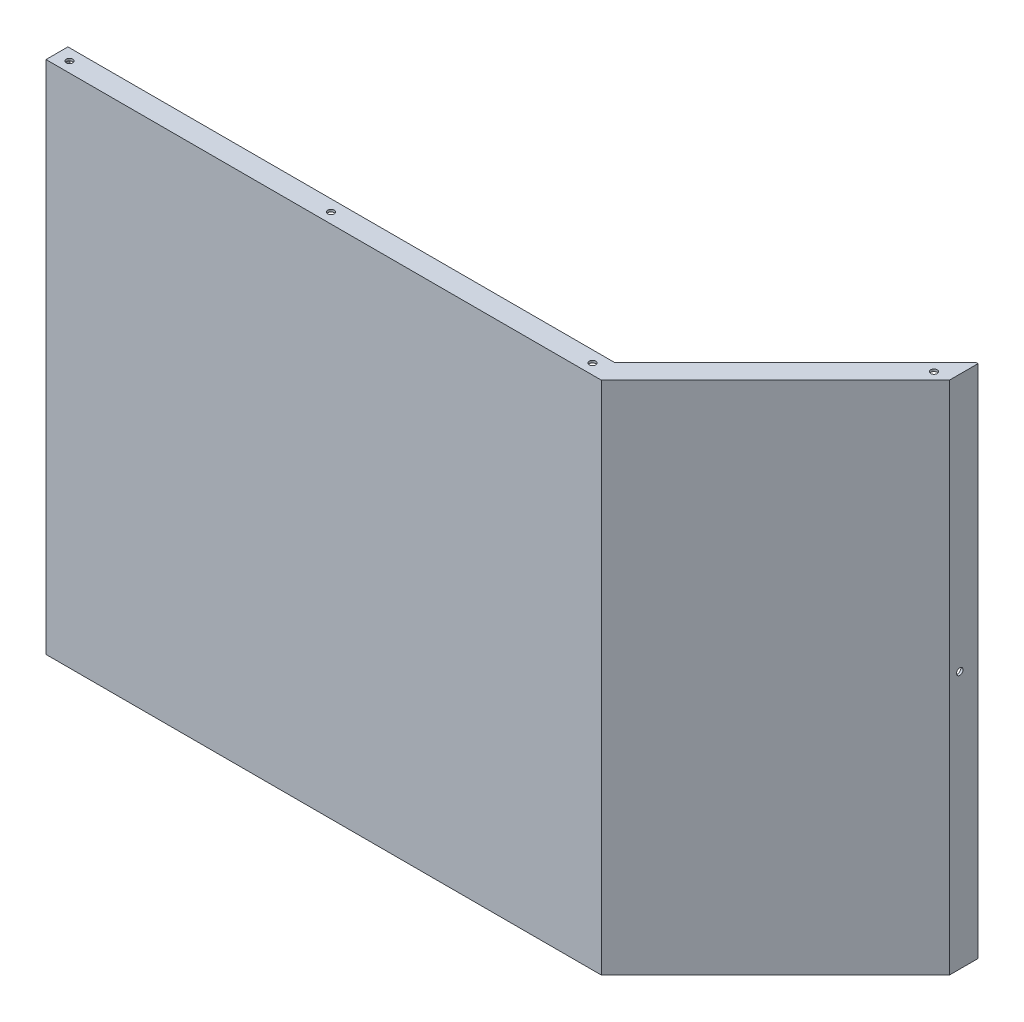
SolidWorks part; units mm, degrees
material "PPS"
ref_plane "Płaszczyzna XY" through (0, 0, 0) normal (0, 0, 1) x (1, 0, 0)
ref_plane "Płaszczyzna XZ" through (0, 0, 0) normal (0, 1, 0) x (1, 0, 0)
ref_plane "Płaszczyzna YZ" through (0, 0, 0) normal (1, 0, 0) x (0, 0, -1)
sketch "Szkic1" plane through (0, 0, 0) normal (0, 1, 0) x (1, 0, 0)
  line L0 (-422.25, 0) -> (0, 0)
  line L1 (0, 0) -> (132, 132)
  line L3 (-424, 0) -> (-424, -1.75)
  line L4 (-424, -1.75) -> (0.7249, -1.75)
  line L5 (133.75, 131.2751) -> (0.7249, -1.75)
  line L6 (-424, 0) -> (-424, 15)
  line L7 (-424, 15) -> (-422.25, 15)
  line L8 (-422.25, 15) -> (-422.25, 0)
  line L9 (132, 132) -> (132, 153.2)
  line L10 (132, 153.2) -> (133.75, 153.2)
  line L11 (133.75, 153.2) -> (133.75, 131.2751)
  dimension "D2" = 424
  dimension "D3" = 1.75
  dimension "D4" = 1.75
  dimension "D5" = 0
  dimension "D6" = 135
  dimension "D7" = 0
  dimension "D8" = 15
  dimension "D9" = 1.75
  dimension "D10" = 15
  dimension "D11" = 1.75
  dimension "D12" = 21.2
  dimension "D13" = 132
extrude "Dodanie-wyciągnięcie1" add sketch "Szkic1" along normal mid plane 394
sketch "Szkic2" plane through (0, -197, 0) normal (0, -1, 0) x (1, 0, 0)
  line L0 (-422.25, -15) -> (-422.25, 0)
  line L1 (-422.25, -15) -> (-424, -15) construction
  line L2 (0, 0) -> (-422.25, 0) construction
  line L3 (-422.25, 0) -> (-422.25, -15) construction
  line L4 (-422.25, 0) -> (0, 0)
  line L5 (0, 0) -> (132, -132)
  line L6 (132, -153.2) -> (132, -132) construction
  line L7 (132, -132) -> (0, 0) construction
  line L8 (132, -132) -> (132, -153.2132)
  line L11 (-422.25, -15) -> (-6.2132, -15)
  line L12 (-6.2132, -15) -> (132, -153.2132)
  dimension "D1" = 15
  dimension "D2" = 135
extrude "Dodanie-wyciągnięcie2" add sketch "Szkic2" against normal blind 1.75
mirror "Lustro1" about plane through (0, 0, 0) normal (0, 1, 0) of "Dodanie-wyciągnięcie2"
sketch "Szkic3" plane through (0, -197, 0) normal (0, -1, 0) x (1, 0, 0)
  line L0 (-424, 1.75) -> (0.7249, 1.75) construction
  line L2 (-424, -15) -> (-424, 1.75) construction
  line L3 (0.7249, 1.75) -> (133.75, -131.2751) construction
  circle A0 centre (-414, -6.25) radius 2.5
  circle A1 centre (-214, -6.25) radius 2.5
  circle A2 centre (-14, -6.25) radius 2.5
  circle A3 centre (122.2215, -131.0603) radius 2.5
  dimension "D1" = 5
  dimension "D2" = 8
  dimension "D3" = 10
  dimension "D4" = 5
  dimension "D5" = 8
  dimension "D6" = 200
  dimension "D7" = 200
  dimension "D8" = 8
  dimension "D9" = 5
  dimension "D10" = 5
  dimension "D11" = 8
  dimension "D12" = 180
extrude "Wytnij-wyciągnięcie1" cut sketch "Szkic3" against normal blind 466
sketch "Szkic4" plane through (133.75, 0, 0) normal (1, 0, 0) x (0, 0, -1)
  line L0 (131.2751, 197) -> (131.2751, -197) construction
  line L1 (131.2751, 197) -> (153.2, 197) construction
  circle A0 centre (139.2751, 0) radius 2.5
  dimension "D1" = 5
  dimension "D3" = 197
  dimension "D2" = 8
extrude "Wytnij-wyciągnięcie2" cut sketch "Szkic4" against normal blind 5
sketch "Szkic5" plane through (-424, 0, 0) normal (-1, 0, 0) x (0, 0, 1)
  line L0 (1.75, 197) -> (1.75, -197) construction
  line L1 (-15, -197) -> (1.75, -197) construction
  circle A0 centre (-6.25, 0) radius 2.5
  dimension "D1" = 5
  dimension "D2" = 8
  dimension "D3" = 197
extrude "Wytnij-wyciągnięcie3" cut sketch "Szkic5" against normal blind 5
